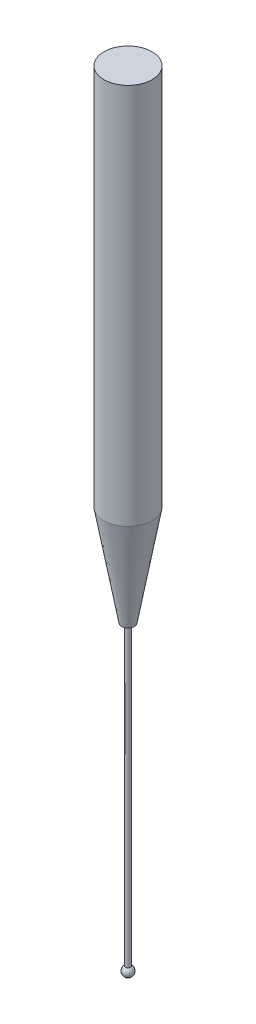
SolidWorks part; units mm, degrees
ref_plane "Front Plane" through (0, 0, 0) normal (0, 0, 1) x (1, 0, 0)
ref_plane "Top Plane" through (0, 0, 0) normal (0, 1, 0) x (1, 0, 0)
ref_plane "Right Plane" through (0, 0, 0) normal (1, 0, 0) x (0, 0, -1)
sketch "Sketch1" plane through (0, 0, 0) normal (0, 0, 1) x (1, 0, 0)
  line L0 (0, -156.1703) -> (0, 7652.3471) construction
  line L1 (0, 0) -> (2.4, 0)
  line L2 (2.4, 0) -> (2.4, -38)
  line L3 (2.4, -38) -> (0.6367, -48)
  line L4 (0.6367, -48) -> (0.2504, -48)
  line L5 (0.2504, -48) -> (0.2504, -77.5672)
  line L6 (0, -78.5) -> (0, 0)
  arc A0 (0, -78.5) -> (0.2504, -77.5672) centre (0, -78) ccw
  dimension "D2" = 78
  dimension "D3" = 1
  dimension "D1" = 4.8
  dimension "D4" = 170
  dimension "D5" = 10
  dimension "D6" = 30
  dimension "D7" = 0.5009
revolve "Revolve1" add sketch "Sketch1" angle 360 about L0
